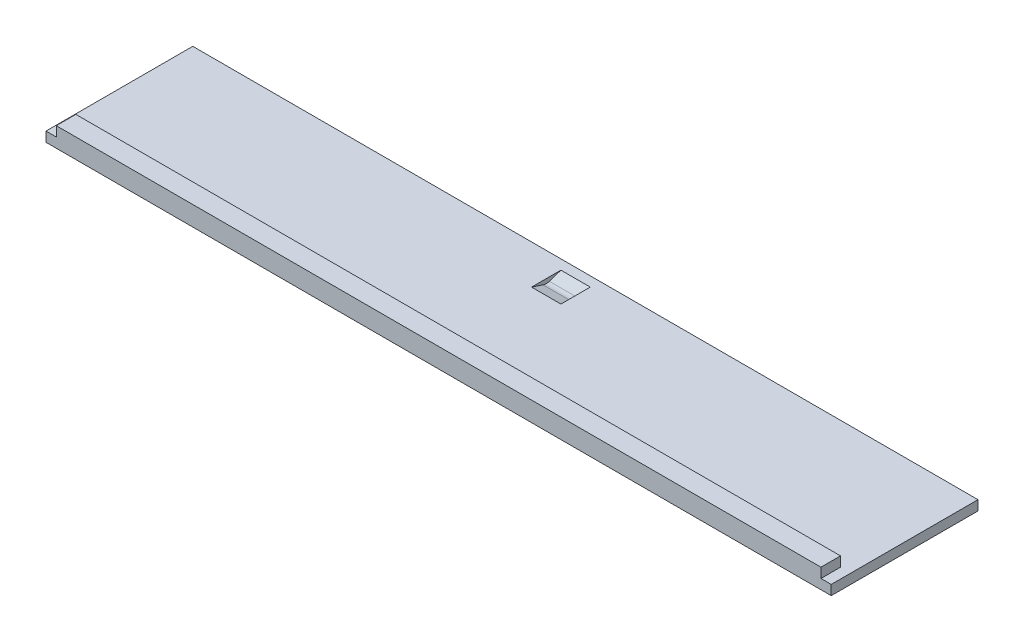
SolidWorks part; units mm, degrees
ref_plane "Front Plane" through (0, 0, 0) normal (0, 0, 1) x (1, 0, 0)
ref_plane "Top Plane" through (0, 0, 0) normal (0, 1, 0) x (1, 0, 0)
ref_plane "Right Plane" through (0, 0, 0) normal (1, 0, 0) x (0, 0, -1)
sketch "Sketch1" plane through (0, 0, 0) normal (0, 1, 0) x (1, 0, 0)
  line L1 (101.9175, -19.05) -> (-101.9175, -19.05)
  line L2 (101.9175, -19.05) -> (101.9175, 19.05)
  line L3 (101.9175, 19.05) -> (-101.9175, 19.05)
  line L4 (-101.9175, -19.05) -> (-101.9175, 19.05)
  line L5 (101.9175, -19.05) -> (-101.9175, 19.05) construction
  line L6 (101.9175, 19.05) -> (-101.9175, -19.05) construction
  point P0 (0, 0)
  dimension "D1" = 38.1
  dimension "D2" = 203.835
extrude "Boss-Extrude1" add sketch "Sketch1" along normal blind 2.54
sketch "Sketch2" plane through (0, 0, 19.05) normal (0, 0, 1) x (1, 0, 0)
  line L0 (-99.2505, 2.54) -> (99.2505, 2.54)
  line L1 (-101.9175, 2.54) -> (101.9175, 2.54) construction
  line L2 (-101.9175, 2.54) -> (-101.9175, 0) construction
  line L3 (101.9175, 2.54) -> (101.9175, 0) construction
  line L4 (-99.2505, 2.54) -> (-99.2505, 5.08)
  line L5 (-99.2505, 5.08) -> (99.2505, 5.08)
  line L6 (99.2505, 5.08) -> (99.2505, 2.54)
  dimension "D1" = 2.667
  dimension "D2" = 2.667
  dimension "D3" = 2.54
extrude "Boss-Extrude2" add sketch "Sketch2" against normal blind 5.08
sketch "Sketch5" plane through (0, 0, 0) normal (1, 0, 0) x (0, 0, -1)
  line L0 (19.05, 2.54) -> (16.51, 2.54) construction
  line L1 (-19.05, 2.54) -> (19.05, 2.54) construction
  line L2 (16.51, 2.54) -> (12.7, 1.27)
  line L5 (12.7, 1.27) -> (12.7, 2.54) construction
  line L6 (8.89, 2.54) -> (16.51, 2.54)
  line L7 (8.89, 2.54) -> (12.7, 1.27)
  dimension "D1" = 2.54
  dimension "D2" = 1.27
  dimension "D3" = 3.81
extrude "Cut-Extrude1" cut sketch "Sketch5" along normal blind 3.81 and the other way blind 3.81
fillet "Fillet2" radius 2.54 1 edges at (0, 1.27, -12.7)
